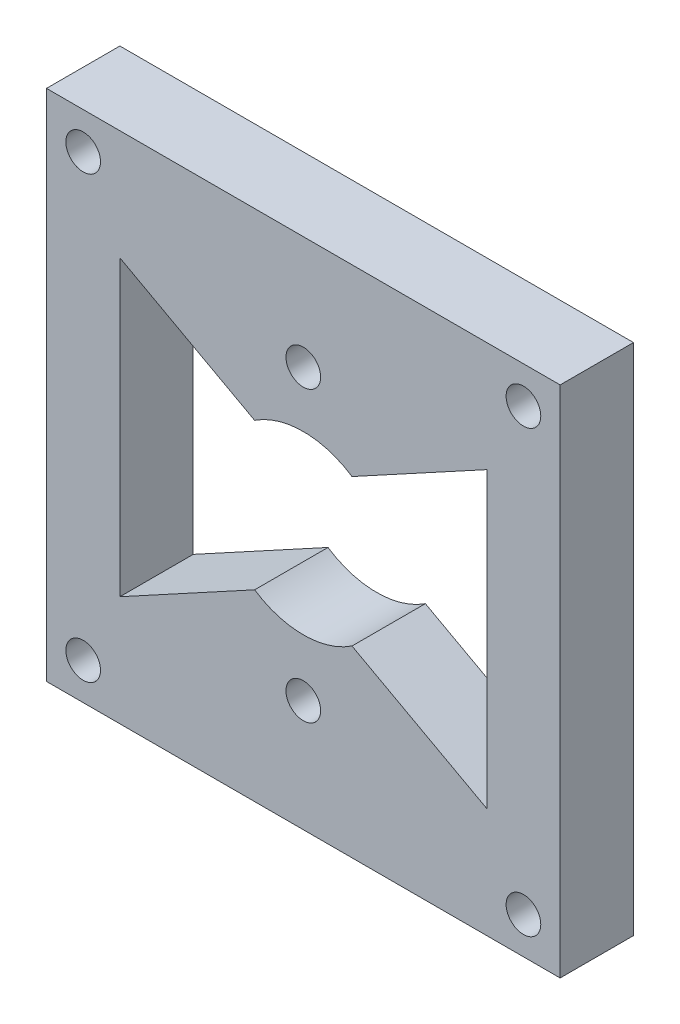
SolidWorks part; units mm, degrees
ref_plane "Front Plane" through (0, 0, 0) normal (0, 0, 1) x (1, 0, 0)
ref_plane "Top Plane" through (0, 0, 0) normal (0, 1, 0) x (1, 0, 0)
ref_plane "Right Plane" through (0, 0, 0) normal (1, 0, 0) x (0, 0, -1)
sketch "Sketch1" plane through (0, 0, 0) normal (0, 0, 1) x (1, 0, 0)
  line L1 (0, 0) -> (44.45, 0)
  line L2 (0, 0) -> (0, 44.45)
  line L3 (0, 44.45) -> (44.45, 44.45)
  line L4 (44.45, 0) -> (44.45, 44.45)
  dimension "D1" = 44.45
  dimension "D2" = 44.45
extrude "Boss-Extrude1" add sketch "Sketch1" along normal blind 6.35
sketch "Sketch2" plane through (0, 0, 6.35) normal (0, 0, 1) x (1, 0, 0)
  line L0 (0, 44.45) -> (0, 0) construction
  line L1 (44.45, 44.45) -> (0, 44.45) construction
  circle A0 centre (22.225, 34.671) radius 1.5
  circle A1 centre (22.225, 9.671) radius 1.5
  dimension "D2" = 3
  dimension "D3" = 3
  dimension "D1" = 25
  dimension "D4" = 22.225
  dimension "D5" = 9.779
  dimension "D6" = 22.225
extrude "Cut-Extrude2" cut sketch "Sketch2" against normal blind 6.35
sketch "Sketch3" plane through (0, 0, 6.35) normal (0, 0, 1) x (1, 0, 0)
  line L0 (0, 44.45) -> (0, 0) construction
  line L1 (44.45, 44.45) -> (0, 44.45) construction
  circle A0 centre (22.225, 22.225) radius 7.62
  point P2 (0, 22.225)
  dimension "D1" = 15.24
  dimension "D2" = 22.225
  dimension "D3" = 22.225
extrude "Cut-Extrude3" cut sketch "Sketch3" against normal blind 6.35 contours A0
sketch "Sketch4" plane through (0, 0, 6.35) normal (0, 0, 1) x (1, 0, 0)
  line L0 (44.45, 44.45) -> (0, 44.45) construction
  line L1 (0, 44.45) -> (0, 0) construction
  line L2 (44.45, 0) -> (44.45, 44.45) construction
  line L3 (0, 0) -> (44.45, 0) construction
  circle A0 centre (3.175, 41.275) radius 1.5
  circle A1 centre (41.275, 41.275) radius 1.5
  circle A2 centre (41.275, 3.175) radius 1.5
  circle A3 centre (3.175, 3.175) radius 1.5
  dimension "D1" = 3
  dimension "D2" = 3
  dimension "D3" = 3
  dimension "D4" = 3
  dimension "D5" = 3.175
  dimension "D6" = 3.175
  dimension "D7" = 3.175
  dimension "D8" = 3.175
  dimension "D9" = 3.175
  dimension "D10" = 3.175
  dimension "D11" = 3.175
  dimension "D12" = 3.175
extrude "Cut-Extrude4" cut sketch "Sketch4" against normal blind 6.35
sketch "Sketch7" plane through (0, 0, 6.35) normal (0, 0, 1) x (1, 0, 0)
  line L0 (38.1, 34.925) -> (38.1, 9.525)
  line L1 (38.1, 9.525) -> (26.4371, 15.875)
  line L2 (22.225, 34.671) -> (22.225, 9.671) construction
  line L3 (26.4371, 28.575) -> (38.1, 34.925)
  line L4 (44.45, 0) -> (44.45, 44.45) construction
  line L5 (0, 0) -> (44.45, 0) construction
  line L6 (6.35, 9.525) -> (18.0129, 15.875)
  line L7 (6.35, 34.925) -> (6.35, 9.525)
  line L8 (18.0129, 28.575) -> (6.35, 34.925)
  circle A0 centre (22.225, 22.225) radius 7.62 construction
  arc A1 (26.4371, 28.575) -> (26.4371, 15.875) centre (22.225, 22.225) cw
  arc A2 (18.0129, 28.575) -> (18.0129, 15.875) centre (22.225, 22.225) ccw
  dimension "D1" = 25.4
  dimension "D2" = 6.35
  dimension "D3" = 9.525
  dimension "D4" = 12.7
extrude "Cut-Extrude5" cut sketch "Sketch7" against normal blind 6.35
